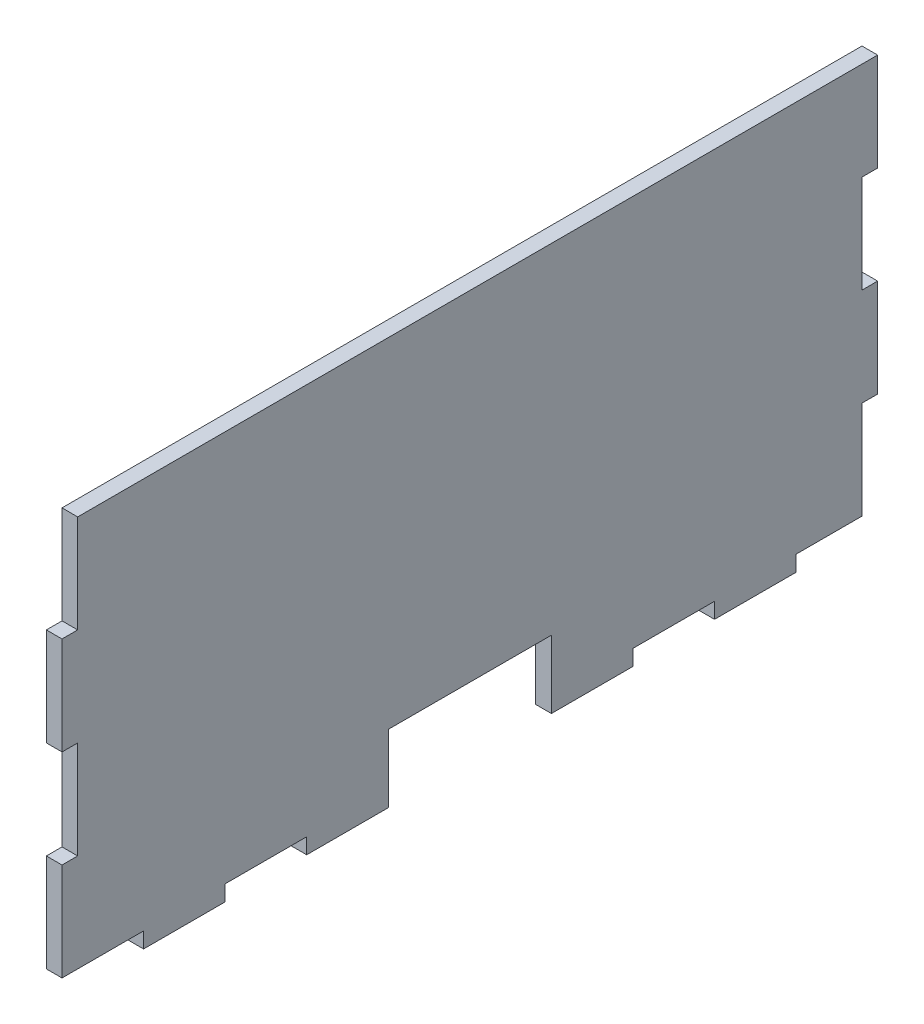
SolidWorks part; units mm, degrees
material "Acrylic (Medium-high impact)"
ref_plane "Front Plane" through (0, 0, 0) normal (0, 0, 1) x (1, 0, 0)
ref_plane "Top Plane" through (0, 0, 0) normal (0, 1, 0) x (1, 0, 0)
ref_plane "Right Plane" through (0, 0, 0) normal (1, 0, 0) x (0, 0, -1)
sketch "Sketch2" plane through (0, 0, 0) normal (1, 0, 0) x (0, 0, -1)
  line L0 (15.875, 3.048) -> (15.875, 0)
  line L1 (3.048, 79.248) -> (158.75, 79.248)
  line L2 (0, 60.198) -> (0, 41.148)
  line L3 (0, 3.048) -> (15.875, 3.048)
  line L4 (158.75, 79.248) -> (158.75, 60.198)
  line L5 (15.875, 0) -> (31.75, 0)
  line L6 (31.75, 0) -> (31.75, 3.048)
  line L7 (47.625, 3.048) -> (47.625, 0)
  line L8 (47.625, 0) -> (63.5, 0)
  line L9 (63.5, 0) -> (63.5, 3.048)
  line L10 (158.75, 60.198) -> (155.702, 60.198)
  line L11 (31.75, 3.048) -> (47.625, 3.048)
  line L13 (95.25, 0) -> (95.25, 3.048)
  line L14 (111.125, 0) -> (95.25, 0)
  line L15 (111.125, 3.048) -> (111.125, 0)
  line L16 (127, 0) -> (127, 3.048)
  line L17 (142.875, 0) -> (127, 0)
  line L18 (142.875, 3.048) -> (142.875, 0)
  line L19 (111.125, 3.048) -> (127, 3.048)
  line L20 (142.875, 3.048) -> (155.702, 3.048)
  line L21 (95.25, 3.048) -> (95.25, 13.208)
  line L22 (95.25, 13.208) -> (63.5, 13.208)
  line L23 (63.5, 13.208) -> (63.5, 3.048)
  line L24 (155.702, 60.198) -> (155.702, 41.148)
  line L25 (155.702, 41.148) -> (158.75, 41.148)
  line L26 (158.75, 22.098) -> (155.702, 22.098)
  line L27 (155.702, 22.098) -> (155.702, 3.048)
  line L28 (158.75, 41.148) -> (158.75, 22.098)
  line L29 (3.048, 79.248) -> (3.048, 60.198)
  line L30 (3.048, 60.198) -> (0, 60.198)
  line L31 (0, 41.148) -> (3.048, 41.148)
  line L32 (3.048, 41.148) -> (3.048, 22.098)
  line L33 (3.048, 22.098) -> (0, 22.098)
  line L34 (0, 22.098) -> (0, 3.048)
  dimension "D1" = 15.875
  dimension "D2" = 3.048
  dimension "D3" = 158.75
  dimension "D4" = 19.05
  dimension "D5" = 10.16
  dimension "D6" = 3.048
  dimension "D7" = 3.048
  dimension "D8" = 19.05
  dimension "D9" = 12.827
  dimension "D10" = 76.2
extrude "Boss-Extrude1" add sketch "Sketch2" along normal blind 3.048
